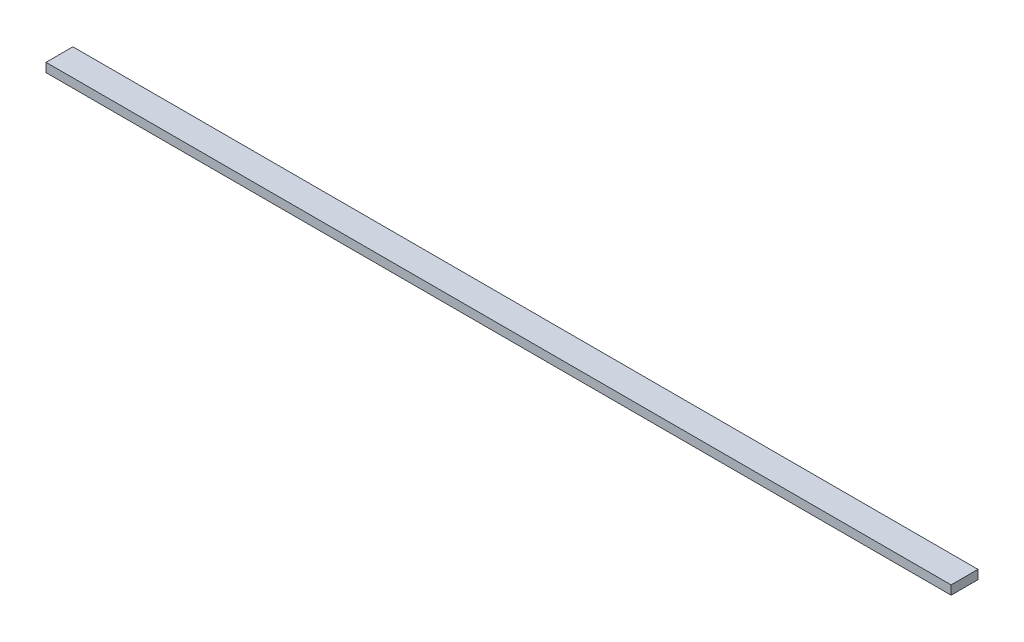
SolidWorks part; units mm, degrees
ref_plane "Front Plane" through (0, 0, 0) normal (0, 0, 1) x (1, 0, 0)
ref_plane "Top Plane" through (0, 0, 0) normal (0, 1, 0) x (1, 0, 0)
ref_plane "Right Plane" through (0, 0, 0) normal (1, 0, 0) x (0, 0, -1)
sketch "Sketch1" plane through (0, 0, 0) normal (0, 1, 0) x (1, 0, 0)
  line L0 (-505, 15) -> (505, -15) construction
  line L1 (-505, 15) -> (505, 15)
  line L2 (-505, 15) -> (-505, -15)
  line L3 (-505, -15) -> (505, -15)
  line L4 (505, 15) -> (505, -15)
  dimension "D1" = 1010
  dimension "D2" = 30
extrude "Boss-Extrude1" add sketch "Sketch1" along normal blind 10
